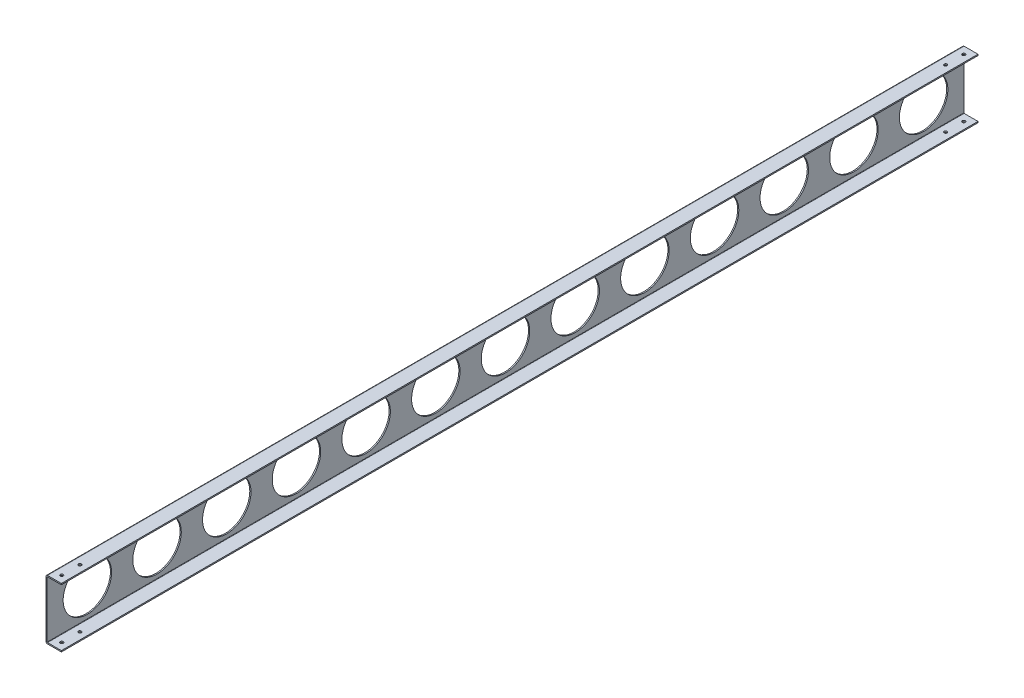
SolidWorks part; units mm, degrees
material "6061-T6 (SS)"
ref_plane "Front" through (0, 0, 0) normal (0, 0, 1) x (1, 0, 0)
ref_plane "Top" through (0, 0, 0) normal (0, 1, 0) x (1, 0, 0)
ref_plane "Right" through (0, 0, 0) normal (1, 0, 0) x (0, 0, -1)
sketch "Sketch1" plane through (0, 0, 0) normal (0, 0, 1) x (1, 0, 0)
  line L0 (0, 46.46) -> (0, -46.46)
  line L1 (0, 0) -> (72.936, 0) construction
  line L2 (2.54, 49) -> (25.4, 49)
  line L3 (2.54, -49) -> (25.4, -49)
  arc A0 (0, -46.46) -> (2.54, -49) centre (2.54, -46.46) ccw
  arc A1 (0, 46.46) -> (2.54, 49) centre (2.54, 46.46) cw
  point P9 (0, -76.2)
  dimension "D3" = 2.54
  dimension "D1" = 98
  dimension "D2" = 25.4
extrude "Extrude-Thin1" add sketch "Sketch1" along normal mid plane 1512.6192 thin thin type one direction reverse wall 2
sketch "Sketch2" plane through (2, 0, 0) normal (1, 0, 0) x (0, 0, -1)
  circle A0 centre (0, 0) radius 40
  dimension "D1" = 80
extrude "Extrude1" cut sketch "Sketch2" against normal through all
pattern_linear "LPattern1" count 7 spacing 115 along (0, 0, 1) of "Extrude1"
pattern_linear "LPattern2" count 7 spacing 115 along (0, 0, -1) of "Extrude1"
sketch "Sketch3" plane through (0, -49, 0) normal (0, -1, 0) x (1, 0, 0)
  line L3 (13.97, 744.3096) -> (13.97, 714.3096) construction
  line L4 (2.54, 756.3096) -> (25.4, 756.3096) construction
  point P4 (13.97, 756.3096)
  dimension "D1" = 12
  dimension "D2" = 30
hole_wizard "#10 Clearance Hole1" positions "Sketch5" profile "Sketch4" hole size "#10" standard "Ansi Inch" end condition through all
sketch "Sketch5" plane through (0, -49, 0) normal (0, -1, 0) x (1, 0, 0)
  point P0 (13.97, 744.3096)
  point P1 (13.97, 714.3096)
sketch "Sketch4" plane through (13.97, -49, 744.3096) normal (1, 0, 0) x (0, 0, -1)
  line L0 (0, 0) -> (0, 98)
  line L1 (0, 98) -> (2.4892, 98)
  line L2 (2.4892, 98) -> (2.4892, 0)
  line L5 (2.4892, 0) -> (0, 0)
  line L11 (0, -6.35) -> (0, 107.95) construction
  dimension "Thru Hole Dia." = 4.9784
  dimension "Thru Hole Depth" = 98
mirror "Mirror1" about plane through (0, 0, 0) normal (0, 0, 1) of "#10 Clearance Hole1"
